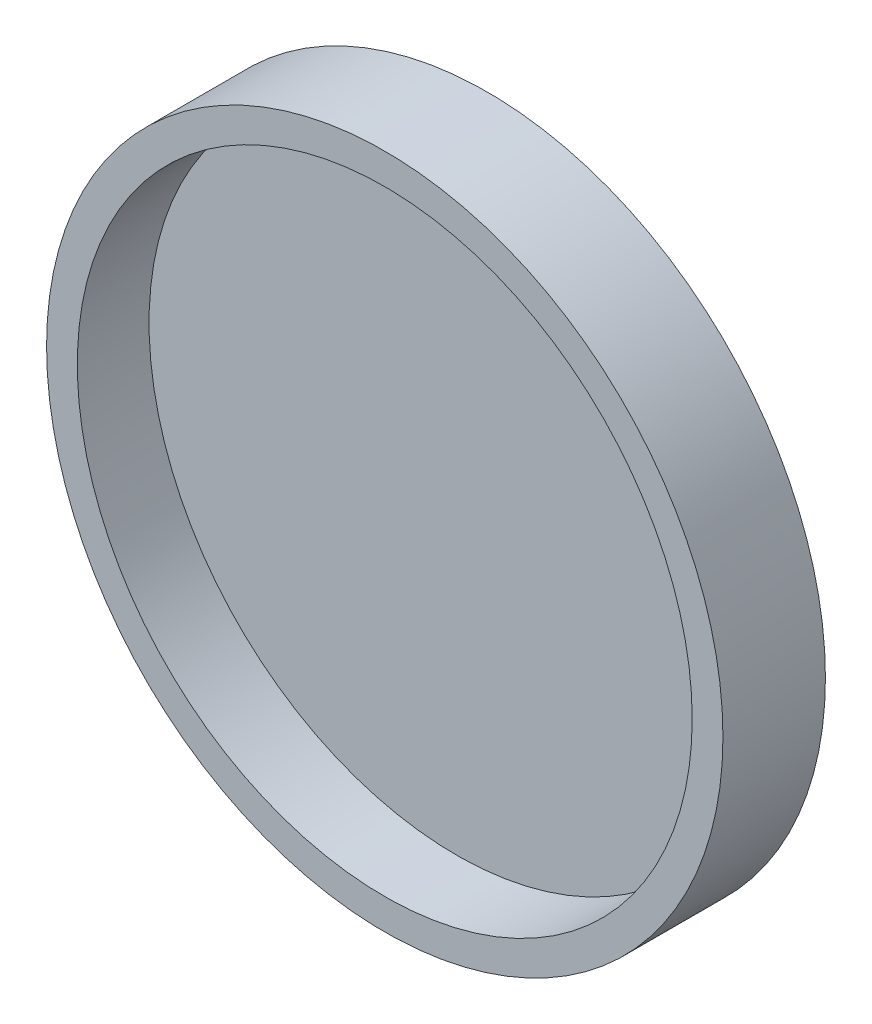
SolidWorks part; units mm, degrees
ref_plane "Front Plane" through (0, 0, 0) normal (0, 0, 1) x (1, 0, 0)
ref_plane "Top Plane" through (0, 0, 0) normal (0, 1, 0) x (1, 0, 0)
ref_plane "Right Plane" through (0, 0, 0) normal (1, 0, 0) x (0, 0, -1)
sketch "Sketch1" plane through (0, 0, 0) normal (0, 0, 1) x (1, 0, 0)
  circle A0 centre (-34.8408, 9.7059) radius 33
  dimension "D1" = 66
extrude "Boss-Extrude1" add sketch "Sketch1" along normal blind 10
shell "Shell1" thickness 3
